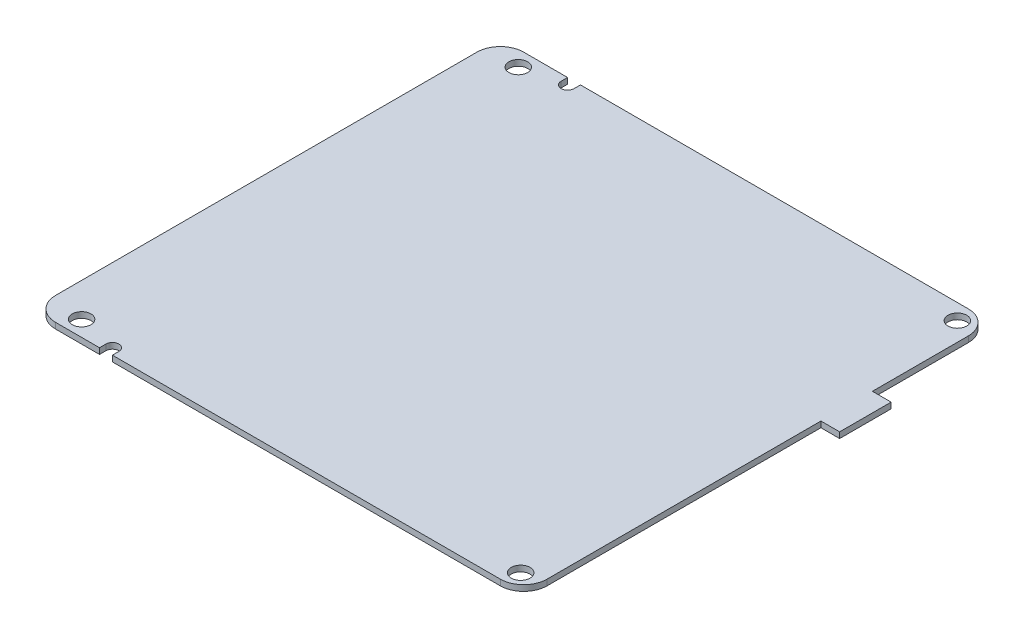
SolidWorks part; units mm, degrees
ref_plane "Front Plane" through (0, 0, 0) normal (0, 0, 1) x (1, 0, 0)
ref_plane "Top Plane" through (0, 0, 0) normal (0, 1, 0) x (1, 0, 0)
ref_plane "Right Plane" through (0, 0, 0) normal (1, 0, 0) x (0, 0, -1)
sketch "Sketch1" plane through (0, 0, 0) normal (0, 1, 0) x (1, 0, 0)
  line L1 (-52.5, 50) -> (52.5, 50)
  line L2 (-52.5, 50) -> (-52.5, -50)
  line L3 (-52.5, -50) -> (52.5, -50)
  line L4 (52.5, 50) -> (52.5, -50)
  line L5 (-52.5, 50) -> (52.5, -50) construction
  line L6 (-52.5, -50) -> (52.5, 50) construction
  line L7 (52.5, 24.5) -> (56.5, 24.5)
  line L8 (52.5, 24.5) -> (52.5, 13.5)
  line L9 (52.5, 13.5) -> (56.5, 13.5)
  line L10 (56.5, 24.5) -> (56.5, 13.5)
  point P0 (0, 0)
  dimension "D1" = 105
  dimension "D2" = 100
  dimension "D3" = 36.5
  dimension "D4" = 11
  dimension "D5" = 4
extrude "Main PCB" add sketch "Sketch1" along normal blind 1.25 contours L4 L1 L2 L3 | L10 L7 L4 L9
fillet "Main PCB rounded corners" radius 5 4 edges at (52.5, 0.625, 50) (-52.5, 0.625, 50) (-52.5, 0.625, -50) (52.5, 0.625, -50)
sketch "Sketch2" plane through (0, 1.25, 0) normal (0, 1, 0) x (1, 0, 0)
  line L0 (-52.5, 0) -> (52.5, 0) construction
  line L3 (0, 50) -> (0, -50) construction
  line L6 (-38.125, -48.625) -> (-38.125, -50)
  line L7 (-35.375, -48.625) -> (-35.375, -50)
  line L8 (-35.375, 48.625) -> (-35.375, 50)
  line L9 (-38.125, 48.625) -> (-38.125, 50)
  line L10 (-47.5, -50) -> (47.5, -50) construction
  line L11 (-52.5, 45) -> (-52.5, -45) construction
  line L12 (-47.5, 50) -> (47.5, 50) construction
  line L15 (52.5, 13.5) -> (52.5, -45) construction
  circle A0 centre (-45.3, -46.65) radius 2
  circle A1 centre (48.5, -46.65) radius 2
  circle A2 centre (48.5, 46.65) radius 2
  circle A3 centre (-45.3, 46.65) radius 2
  circle A4 centre (-36.75, -48.625) radius 1.375
  circle A5 centre (-36.75, 48.625) radius 1.375
  point P2 (0, 0)
  point P5 (0, 0)
  point P10 (0, 0)
  point P11 (0, 0)
  point P32 (48.5, -46.65)
  dimension "D1" = 93.8
  dimension "D3" = 4
  dimension "D4" = 2.75
  dimension "D2" = 93.3
  dimension "D5" = 15.75
  dimension "D6" = 4
extrude "Main PCB holes" cut sketch "Sketch2" against normal up to next
